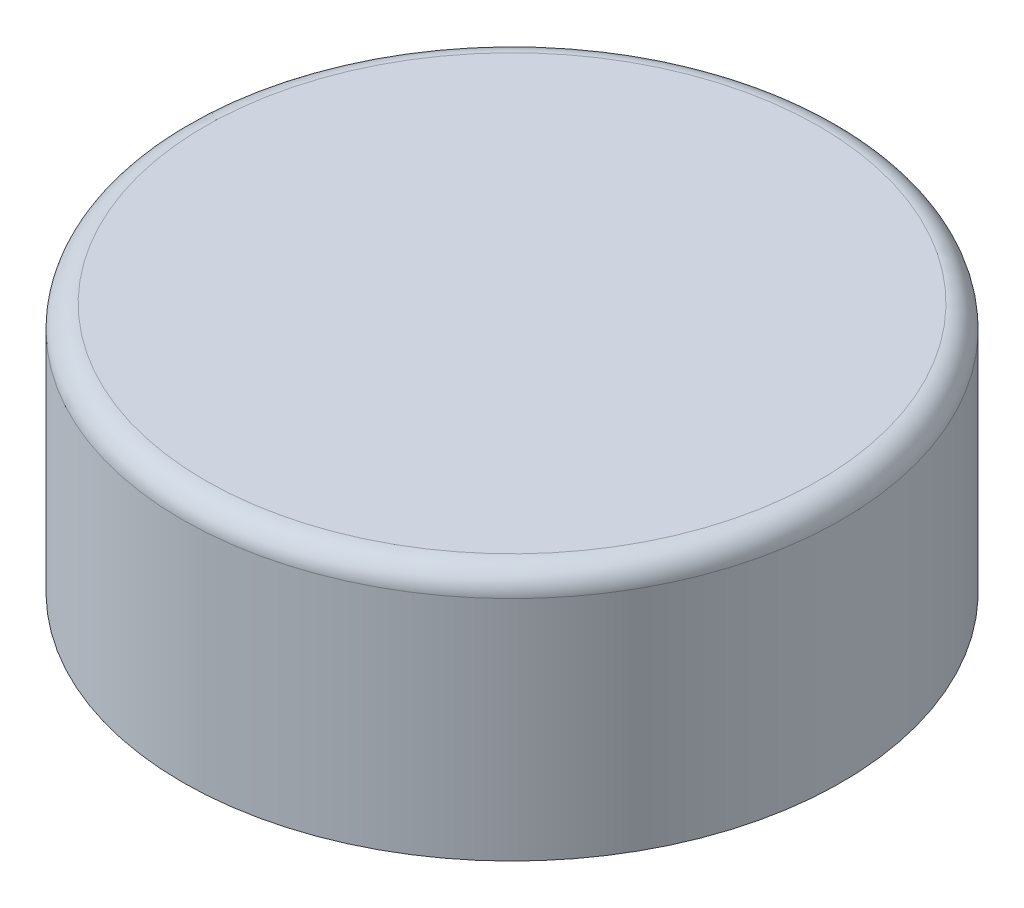
SolidWorks part; units mm, degrees
material "PMMA"
ref_plane "Front Plane" through (0, 0, 0) normal (0, 0, 1) x (1, 0, 0)
ref_plane "Top Plane" through (0, 0, 0) normal (0, 1, 0) x (1, 0, 0)
ref_plane "Right Plane" through (0, 0, 0) normal (1, 0, 0) x (0, 0, -1)
sketch "Sketch1" plane through (0, 0, 0) normal (0, 1, 0) x (1, 0, 0)
  circle A0 centre (0, 0) radius 1.45
  dimension "D1" = 2.9
extrude "Boss-Extrude1" add sketch "Sketch1" along normal blind 1.1
fillet "Fillet1" radius 0.1 1 edges at (0, 1.1, 1.45)
